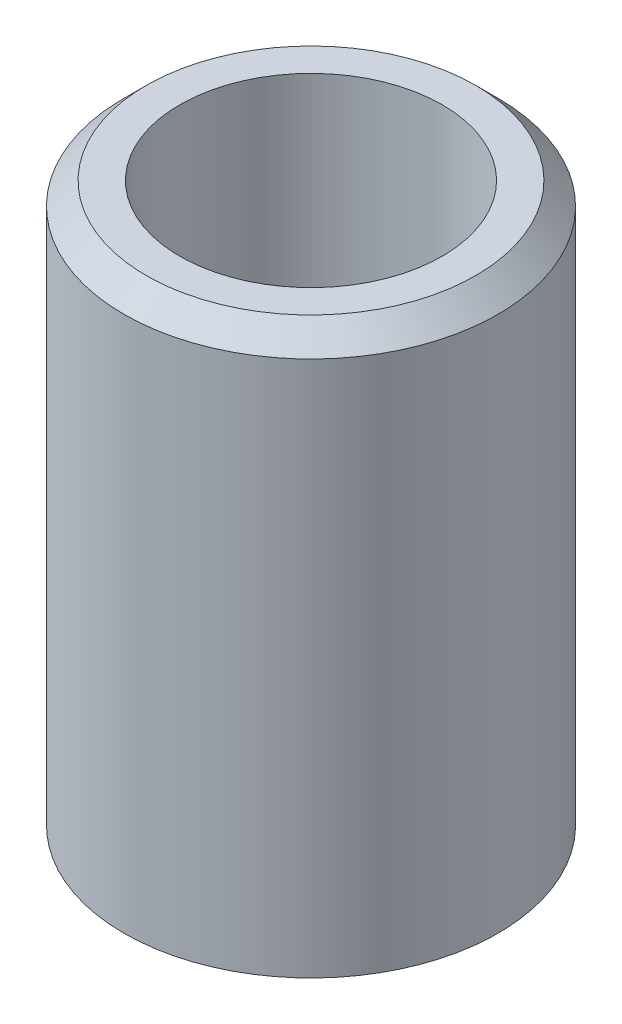
SolidWorks part; units mm, degrees
material "Brass"
ref_plane "Front Plane" through (0, 0, 0) normal (0, 0, 1) x (1, 0, 0)
ref_plane "Top Plane" through (0, 0, 0) normal (0, 1, 0) x (1, 0, 0)
ref_plane "Right Plane" through (0, 0, 0) normal (1, 0, 0) x (0, 0, -1)
sketch "Sketch2" plane through (0, 0, 0) normal (0, 0, 1) x (1, 0, 0)
  line L0 (0, 0) -> (0, 51.583) construction
  line L2 (-8.375, 0) -> (-5.875, 0)
  line L3 (-8.375, 0) -> (-8.375, 25)
  line L4 (-8.375, 25) -> (-5.875, 25)
  line L5 (-5.875, 0) -> (-5.875, 25)
  point P7 (0, 0)
  dimension "D1" = 5.875
  dimension "D2" = 2.5
  dimension "25" = 25
revolve "Revolve1" add sketch "Sketch2" angle 360 about L0
chamfer "Chamfer1" distance 1 angle 45 1 edges at (0, 25, -8.375)
equation "\"D1@Sketch2\"=(11.7+0.05)/2"
